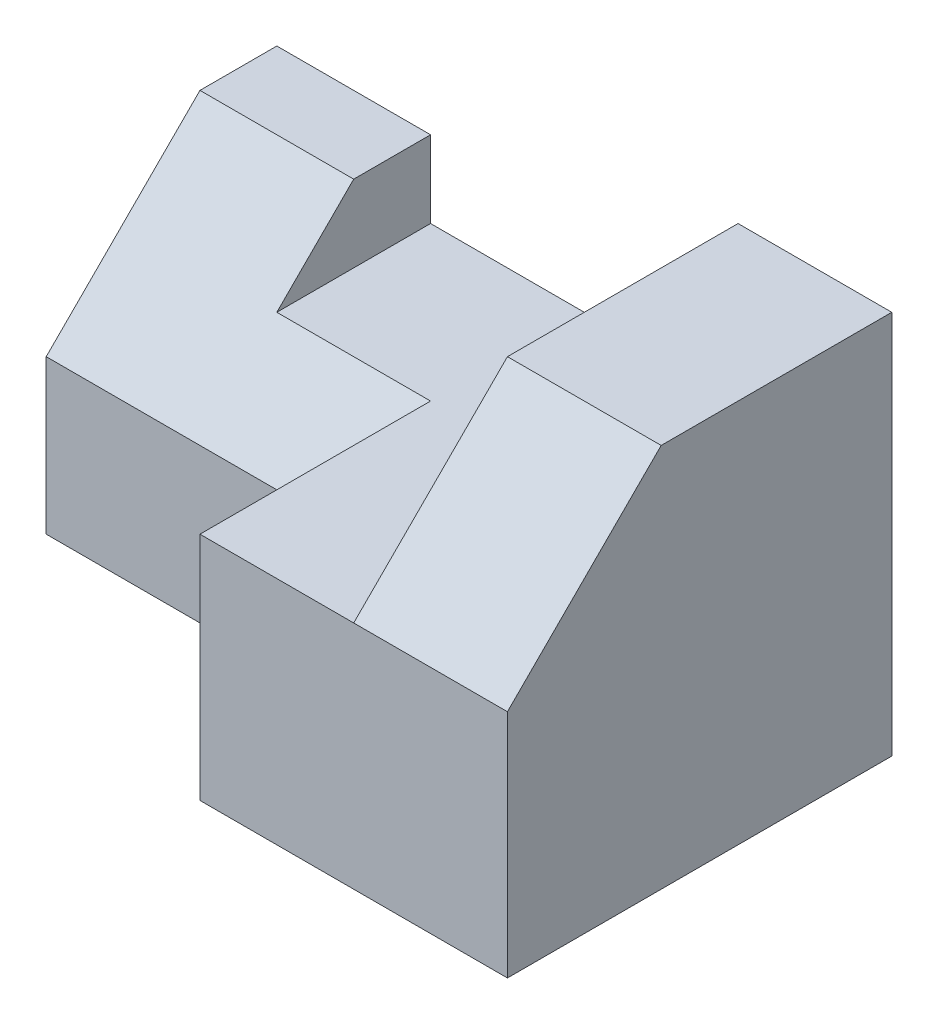
SolidWorks part; units mm, degrees
ref_plane "Front Plane" through (0, 0, 0) normal (0, 0, 1) x (1, 0, 0)
ref_plane "Top Plane" through (0, 0, 0) normal (0, 1, 0) x (1, 0, 0)
ref_plane "Right Plane" through (0, 0, 0) normal (1, 0, 0) x (0, 0, -1)
sketch "Sketch1" plane through (0, 0, 0) normal (0, 1, 0) x (1, 0, 0)
  line L1 (0, 0) -> (80, 0)
  line L2 (0, 0) -> (0, 50)
  line L3 (0, 50) -> (80, 50)
  line L4 (80, 0) -> (80, 50)
  dimension "D1" = 80
  dimension "D2" = 50
extrude "Boss-Extrude1" add sketch "Sketch1" along normal blind 30
sketch "Sketch2" plane through (0, 30, 0) normal (0, 1, 0) x (1, 0, 0)
  line L1 (0, 0) -> (40, 0)
  line L2 (0, 0) -> (0, 20)
  line L3 (0, 20) -> (40, 20)
  line L4 (40, 0) -> (40, 20)
  dimension "D1" = 20
  dimension "D2" = 40
extrude "Cut-Extrude1" cut sketch "Sketch2" against normal blind 30
sketch "Sketch3" plane through (0, 30, 0) normal (0, 1, 0) x (1, 0, 0)
  line L0 (40, 0) -> (80, 0) construction
  line L1 (80, 50) -> (60, 50)
  line L2 (80, 50) -> (80, 0)
  line L3 (80, 0) -> (60, 0)
  line L4 (60, 50) -> (60, 0)
  dimension "D1" = 20
  dimension "D2" = 0
extrude "Boss-Extrude2" add sketch "Sketch3" along normal blind 20
sketch "Sketch4" plane through (80, 0, 0) normal (1, 0, 0) x (0, 0, -1)
  line L0 (20, 50) -> (0, 30)
  line L1 (0, 50) -> (50, 50) construction
  line L2 (0, 50) -> (0, 0) construction
  line L3 (0, 30) -> (0, 50)
  line L4 (0, 50) -> (20, 50)
  dimension "D1" = 20
  dimension "D2" = 20
extrude "Cut-Extrude2" cut sketch "Sketch4" against normal blind 20
sketch "Sketch5" plane through (0, 0, 0) normal (-1, 0, 0) x (0, 0, 1)
  line L0 (-30, 30) -> (-20, 20)
  line L1 (-50, 30) -> (-20, 30) construction
  line L2 (-20, 0) -> (-20, 30) construction
  line L3 (-20, 20) -> (-20, 30)
  line L4 (-20, 30) -> (-30, 30)
  dimension "D1" = 10
  dimension "D2" = 10
extrude "Cut-Extrude4" cut sketch "Sketch5" against normal blind 40
sketch "Sketch6" plane through (0, 0, 0) normal (-1, 0, 0) x (0, 0, 1)
  line L0 (-50, 30) -> (-50, 40)
  line L1 (-50, 40) -> (-40, 40)
  line L2 (-40, 40) -> (-30, 30)
  line L8 (-20, 0) -> (-20, 20)
  line L9 (-20, 20) -> (-30, 30)
  line L10 (-30, 30) -> (-50, 30)
  line L11 (-50, 30) -> (-50, 0)
  line L12 (-50, 0) -> (-20, 0)
  line L13 (-20, 0) -> (-20, 20)
  line L14 (-20, 20) -> (-30, 30)
  line L16 (-50, 30) -> (-50, 0)
  line L17 (-50, 0) -> (-20, 0)
  dimension "D1" = 10
  dimension "D2" = 10
  dimension "D3" = 0
extrude "Boss-Extrude3" add sketch "Sketch6" against normal blind 20
equation "\"A\"=20"
